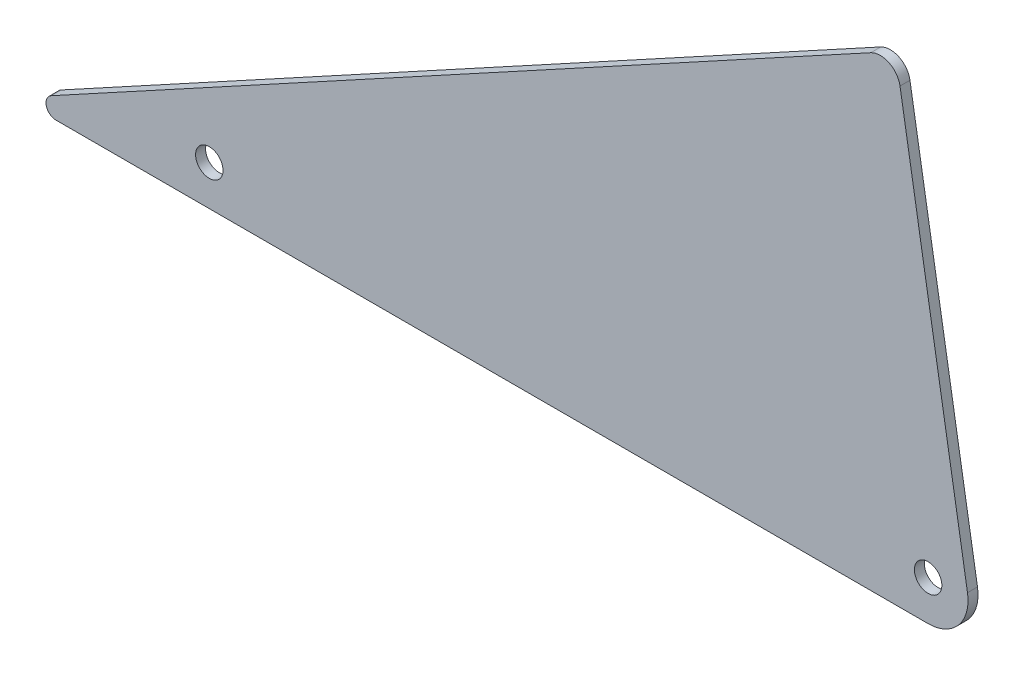
SolidWorks part; units mm, degrees
ref_plane "Front Plane" through (0, 0, 0) normal (0, 0, 1) x (1, 0, 0)
ref_plane "Top Plane" through (0, 0, 0) normal (0, 1, 0) x (1, 0, 0)
ref_plane "Right Plane" through (0, 0, 0) normal (1, 0, 0) x (0, 0, -1)
sketch "Sketch1" plane through (0, 0, 0) normal (0, 0, 1) x (1, 0, 0)
  line L0 (0, 0) -> (-152.4, 0)
  line L1 (-152.4, 0) -> (-12.7, 76.2)
  line L2 (-12.7, 76.2) -> (0, 0)
  line L3 (-7.4959, 6.35) -> (0, 0) construction
  circle A0 centre (-7.4959, 6.35) radius 2.1828
  circle A1 centre (-121.7959, 6.35) radius 2.1828
  dimension "D5" = 4.3656
  dimension "D6" = 4.3656
  dimension "D1" = 152.4
  dimension "D2" = 76.2
  dimension "D3" = 12.7
  dimension "D4" = 6.35
  dimension "D7" = 114.3
extrude "Boss-Extrude1" add sketch "Sketch1" along normal mid plane 1.5875
fillet "Fillet1" radius 6.35 1 edges at (0, 0, 0)
fillet "Fillet2" radius 3.175 1 edges at (-12.7, 76.2, 0)
fillet "Fillet3" radius 1.5875 1 edges at (-152.4, 0, 0)
